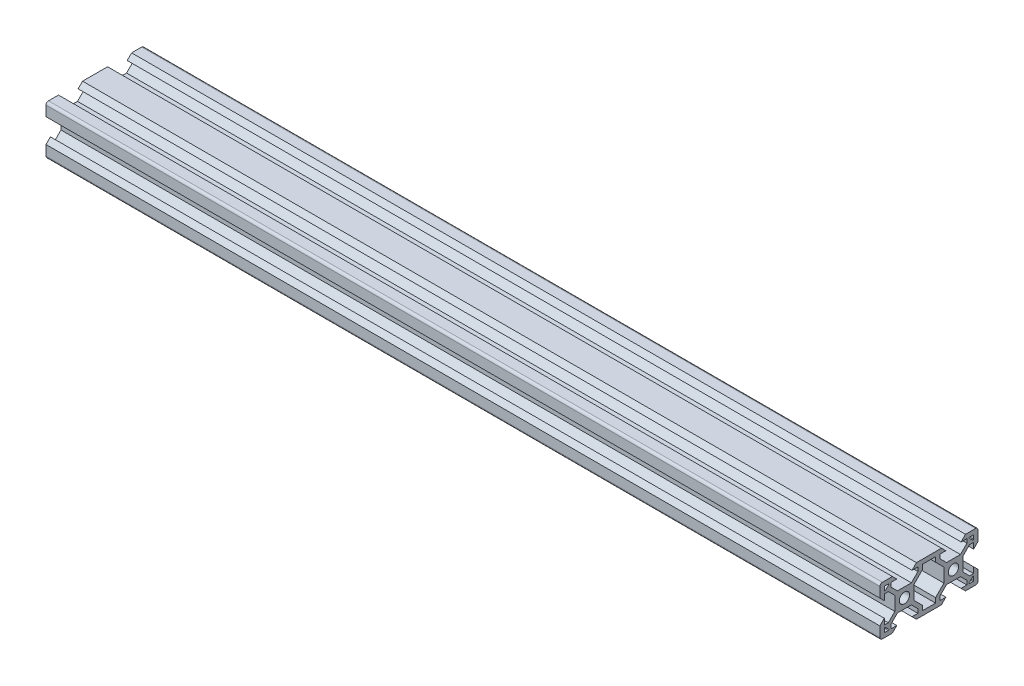
SolidWorks part; units mm, degrees
material "1060 Alloy"
ref_plane "Front Plane" through (0, 0, 0) normal (0, 0, 1) x (1, 0, 0)
ref_plane "Top Plane" through (0, 0, 0) normal (0, 1, 0) x (1, 0, 0)
ref_plane "Right Plane" through (0, 0, 0) normal (1, 0, 0) x (0, 0, -1)
sketch "Sketch4" plane through (0, 0, 0) normal (1, 0, 0) x (0, 0, -1)
  line L0 (-19.2399, 7.0114) -> (20.7601, 7.0114) construction
  dimension "D1" = 40
sketch "Sketch5" plane through (0, 0, 0) normal (1, 0, 0) x (0, 0, -1)
  line L0 (-19.998, 4.9) -> (-18.198, 3.1)
  line L1 (-18.198, 3.1) -> (-18.198, 5.4993)
  line L2 (-18.198, 5.4993) -> (-16.558, 5.4993)
  line L3 (-16.558, 5.4993) -> (-13.9, 2.8413)
  line L4 (-13.9, 2.8413) -> (-13.9, -2.8387)
  line L5 (-13.9, -2.8387) -> (-16.558, -5.4967)
  line L6 (-16.558, -5.4967) -> (-18.198, -5.4967)
  line L7 (-18.198, -5.4967) -> (-18.198, -3.1)
  line L8 (-18.198, -3.1) -> (-19.998, -4.9)
  line L9 (-19.998, -4.9) -> (-19.998, -9)
  line L10 (-18.998, -10) -> (-14.9, -10)
  line L11 (-14.9, -10) -> (-13.1, -8.2)
  line L12 (-13.1, -8.2) -> (-15.5, -8.2)
  line L13 (-15.5, -8.2) -> (-15.5, -6.56)
  line L14 (-15.5, -6.56) -> (-12.84, -3.9)
  line L15 (-12.84, -3.9) -> (-7.16, -3.9)
  line L16 (-7.16, -3.9) -> (-4.5, -6.56)
  line L17 (-4.5, -6.56) -> (-4.5, -8.2)
  line L18 (-4.5, -8.2) -> (-6.9, -8.2)
  line L19 (-6.9, -8.2) -> (-5.1, -10)
  line L20 (-5.1, -10) -> (5.1, -10)
  line L21 (5.1, -10) -> (6.9, -8.2)
  line L22 (6.9, -8.2) -> (4.496, -8.2)
  line L23 (4.496, -8.2) -> (4.496, -6.56)
  line L24 (4.496, -6.56) -> (7.156, -3.9)
  line L25 (7.156, -3.9) -> (12.836, -3.9)
  line L26 (12.836, -3.9) -> (15.496, -6.56)
  line L27 (15.496, -6.56) -> (15.496, -8.2)
  line L28 (15.496, -8.2) -> (13.1, -8.2)
  line L29 (13.1, -8.2) -> (14.9, -10)
  line L30 (14.9, -10) -> (19.002, -10)
  line L31 (20.002, -9) -> (20.002, -4.9)
  line L32 (20.002, -4.9) -> (18.202, -3.1)
  line L33 (18.202, -3.1) -> (18.202, -5.5046)
  line L34 (18.202, -5.5046) -> (16.562, -5.5046)
  line L35 (16.562, -5.5046) -> (13.9, -2.8426)
  line L36 (13.9, -2.8426) -> (13.9, 2.8374)
  line L37 (13.9, 2.8374) -> (16.562, 5.4993)
  line L38 (16.562, 5.4993) -> (18.202, 5.4993)
  line L39 (18.202, 5.4993) -> (18.202, 3.1)
  line L40 (18.202, 3.1) -> (20.002, 4.9)
  line L41 (20.002, 4.9) -> (20.002, 9)
  line L42 (19.002, 10) -> (14.9, 10)
  line L43 (14.9, 10) -> (13.1, 8.2)
  line L44 (13.1, 8.2) -> (15.5013, 8.2)
  line L45 (15.5013, 8.2) -> (15.5013, 6.56)
  line L46 (15.5013, 6.56) -> (12.8413, 3.9)
  line L47 (12.8413, 3.9) -> (7.1613, 3.9)
  line L48 (7.1613, 3.9) -> (4.5013, 6.56)
  line L49 (4.5013, 6.56) -> (4.5013, 8.2)
  line L50 (4.5013, 8.2) -> (6.9, 8.2)
  line L51 (6.9, 8.2) -> (5.1, 10)
  line L52 (5.1, 10) -> (-5.1, 10)
  line L53 (-5.1, 10) -> (-6.9, 8.2)
  line L54 (-6.9, 8.2) -> (-4.5013, 8.2)
  line L55 (-4.5013, 8.2) -> (-4.5013, 6.56)
  line L56 (-4.5013, 6.56) -> (-7.1613, 3.9)
  line L57 (-7.1613, 3.9) -> (-12.8413, 3.9)
  line L58 (-12.8413, 3.9) -> (-15.5013, 6.56)
  line L59 (-15.5013, 6.56) -> (-15.5013, 8.2)
  line L60 (-15.5013, 8.2) -> (-13.1, 8.2)
  line L61 (-13.1, 8.2) -> (-14.9, 10)
  line L62 (-14.9, 10) -> (-18.998, 10)
  line L63 (-19.998, 9) -> (-19.998, 4.9)
  line L64 (6.1, -2.84) -> (6.1, 2.84)
  line L65 (6.1, 2.84) -> (2.7, 6.24)
  line L66 (2.7, 6.24) -> (2.7, 8.2)
  line L67 (2.7, 8.2) -> (-2.7, 8.2)
  line L68 (-2.7, 8.2) -> (-2.7, 6.24)
  line L69 (-2.7, 6.24) -> (-6.1, 2.84)
  line L70 (-6.1, 2.84) -> (-6.1, -2.84)
  line L71 (-6.1, -2.84) -> (-2.7, -6.24)
  line L72 (-2.7, -6.24) -> (-2.7, -8.2)
  line L73 (-2.7, -8.2) -> (2.7, -8.2)
  line L74 (2.7, -8.2) -> (2.7, -6.24)
  line L75 (2.7, -6.24) -> (6.1, -2.84)
  line L76 (0, -8.2) -> (0, 8.2) construction
  line L77 (6.1, 0) -> (-6.1, 0) construction
  line L78 (16.562, 5.4993) -> (15.5013, 6.56) construction
  line L79 (16.5713, 8.2) -> (18.002, 8.2)
  line L81 (17.8606, 6.4279) -> (16.4299, 7.8586)
  line L82 (18.202, 8) -> (18.202, 6.5693)
  line L83 (18.002, 6.5693) -> (18.002, 8) construction
  line L84 (18.002, 8) -> (16.5713, 8) construction
  line L85 (16.5713, 8) -> (18.002, 6.5693) construction
  line L86 (16.5713, -8.2) -> (18.002, -8.2)
  line L87 (18.202, -8) -> (18.202, -6.5693)
  line L88 (17.8606, -6.4279) -> (16.4299, -7.8586)
  line L89 (-17.8606, 6.4279) -> (-16.4299, 7.8586)
  line L90 (-16.5713, 8.2) -> (-18.002, 8.2)
  line L91 (-18.202, 8) -> (-18.202, 6.5693)
  line L92 (-16.5713, -8.2) -> (-18.002, -8.2)
  line L93 (-17.8606, -6.4279) -> (-16.4299, -7.8586)
  line L94 (-18.202, -8) -> (-18.202, -6.5693)
  circle A0 centre (-10, 0) radius 2.1
  circle A1 centre (10, 0) radius 2.1
  arc A2 (-19.998, -9) -> (-18.998, -10) centre (-18.998, -9) ccw
  arc A5 (-18.998, 10) -> (-19.998, 9) centre (-18.998, 9) ccw
  arc A6 (20.002, -9) -> (19.002, -10) centre (19.002, -9) cw
  arc A7 (20.002, 9) -> (19.002, 10) centre (19.002, 9) ccw
  arc A8 (18.002, 8.2) -> (18.202, 8) centre (18.002, 8) cw
  arc A10 (16.4299, 7.8586) -> (16.5713, 8.2) centre (16.5713, 8) cw
  arc A12 (18.202, 6.5693) -> (17.8606, 6.4279) centre (18.002, 6.5693) cw
  arc A13 (16.4299, -7.8586) -> (16.5713, -8.2) centre (16.5713, -8) ccw
  arc A14 (18.002, -8.2) -> (18.202, -8) centre (18.002, -8) ccw
  arc A15 (18.202, -6.5693) -> (17.8606, -6.4279) centre (18.002, -6.5693) ccw
  arc A16 (-18.202, 6.5693) -> (-17.8606, 6.4279) centre (-18.002, 6.5693) ccw
  arc A17 (-16.4299, 7.8586) -> (-16.5713, 8.2) centre (-16.5713, 8) ccw
  arc A18 (-18.002, 8.2) -> (-18.202, 8) centre (-18.002, 8) ccw
  arc A19 (-18.002, -8.2) -> (-18.202, -8) centre (-18.002, -8) cw
  arc A20 (-16.4299, -7.8586) -> (-16.5713, -8.2) centre (-16.5713, -8) cw
  arc A21 (-18.202, -6.5693) -> (-17.8606, -6.4279) centre (-18.002, -6.5693) cw
  dimension "D1" = 4.2
  dimension "D20" = 3.9
  dimension "D27" = 1
  dimension "D40" = 1
  dimension "D41" = 1
  dimension "D42" = 1
  dimension "D45" = 0.2
  dimension "D47" = 1.07
  dimension "D48" = 1.07
  dimension "D49" = 0.2
  dimension "D2" = 20
  dimension "D3" = 10
  dimension "D4" = 5.68
  dimension "D5" = 5.4
  dimension "D6" = 1.96
  dimension "D7" = 45
  dimension "D8" = 1.8
  dimension "D9" = 1.64
  dimension "D10" = 1.8
  dimension "D11" = 40
  dimension "D12" = 20
  dimension "D13" = 3.9
  dimension "D14" = 1.5
  dimension "D15" = 1.5
  dimension "D16" = 3.9
  dimension "D17" = 3.9
  dimension "D18" = 3.9
  dimension "D19" = 3.9
  dimension "D21" = 1.5
  dimension "D22" = 1.5
  dimension "D23" = 1.64
  dimension "D24" = 45
  dimension "D25" = 1.5
  dimension "D26" = 1.8
  dimension "D28" = 6.2
  dimension "D29" = 6.2
  dimension "D30" = 6.2
  dimension "D31" = 6.2
  dimension "D32" = 6.2
  dimension "D33" = 3.1
  dimension "D34" = 3.1
  dimension "D35" = 3.1
  dimension "D36" = 3.1
  dimension "D37" = 6.2
  dimension "D38" = 3.1
  dimension "D39" = 3.1
  dimension "D43" = 1.64
  dimension "D44" = 135
  dimension "D46" = 45
extrude "Boss-Extrude1" add sketch "Sketch5" along normal mid plane 340
